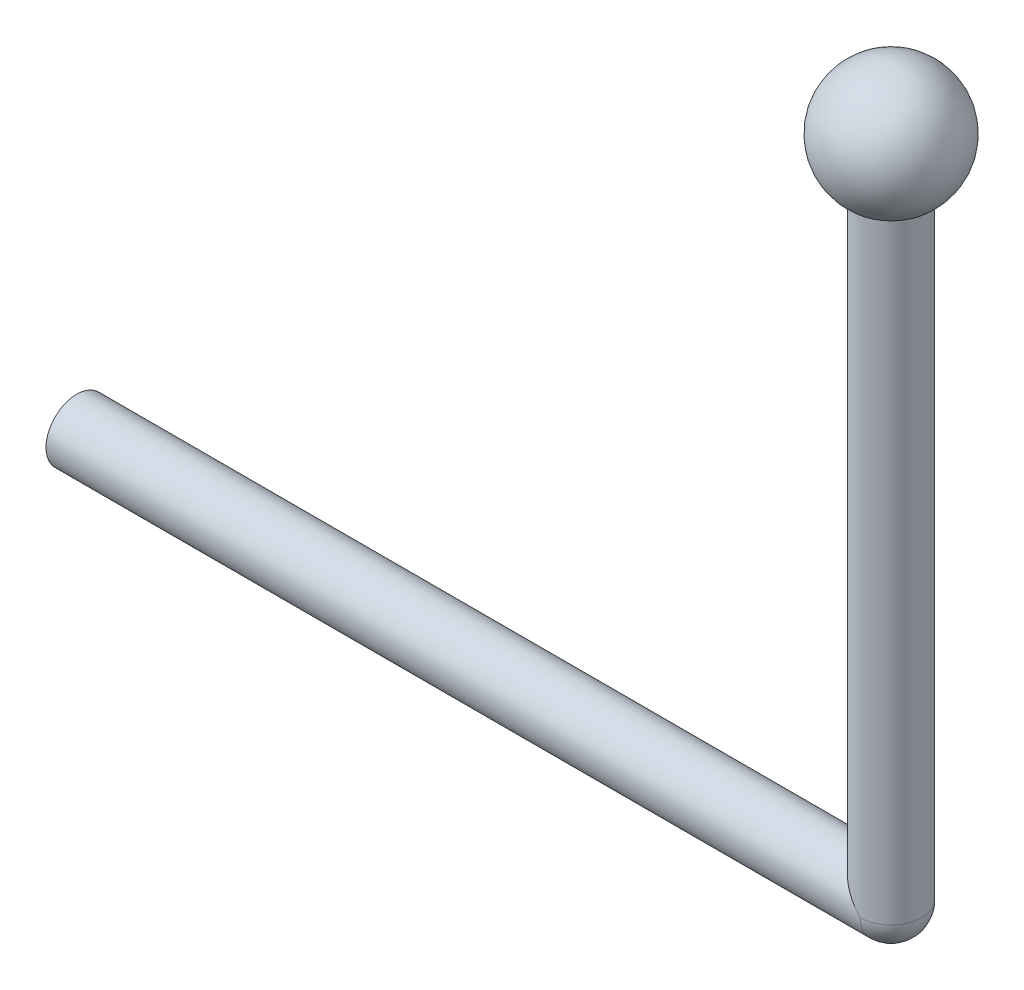
SolidWorks part; units mm, degrees
material "AISI 316 退火不锈钢条 (SS)"
ref_plane "前视基准面" through (0, 0, 0) normal (0, 0, 1) x (1, 0, 0)
ref_plane "上视基准面" through (0, 0, 0) normal (0, 1, 0) x (1, 0, 0)
ref_plane "右视基准面" through (0, 0, 0) normal (1, 0, 0) x (0, 0, -1)
sketch "草图1" plane through (0, 0, 0) normal (0, 0, 1) x (1, 0, 0)
  line L0 (0, 0) -> (0, -4)
  line L1 (0, -4) -> (0, -49)
  line L2 (0, -49) -> (9.6403, -55.4018) construction
  line L3 (-2, 0) -> (-2, -4)
  line L4 (-2, -4) -> (-2, -50.0727)
  line L5 (-2, -50.0727) -> (8.9504, -57.3445) construction
  line L6 (64.448, -62.7045) -> (64.6403, -60.7138)
  line L7 (0, 0) -> (-2, 0)
  line L8 (0, 0) -> (0, 4)
  line L9 (0, -49) -> (60, -49)
  line L10 (-2, 0) -> (-2, -4)
  line L11 (9.6403, -55.4018) -> (64.6403, -60.7138) construction
  line L12 (8.9504, -57.3445) -> (64.448, -62.7045) construction
  line L13 (-2, -4) -> (-2, -51)
  line L14 (-2, -51) -> (60, -51)
  circle A0 centre (0, 0) radius 4
  point P3 (0, -51.839)
  point P7 (6.2479, -54.3857)
  dimension "D1" = 8
  dimension "D2" = 45
  dimension "D3" = 2
  dimension "D5" = 60
  dimension "D4" = 2
revolve "旋转3" add sketch "草图1" angle 360 about L1
sketch "草图3" plane through (0, 0, 0) normal (0, 0, 1) x (1, 0, 0)
  line L0 (0, 0) -> (0, -2)
  line L1 (0, -2) -> (0, -45)
  line L2 (-2, -43) -> (0, -43)
  line L3 (-2, 0) -> (-2, -2)
  line L4 (-2, -2) -> (-2, -43)
  line L6 (-60, -45) -> (-60, -43)
  line L7 (0, 0) -> (-2, 0)
  line L9 (-2, -43) -> (-60, -43) construction
  line L10 (0, -45) -> (-60, -45) construction
  circle A0 centre (0, 0) radius 2
  dimension "D1" = 4
  dimension "D2" = 45
  dimension "D3" = 60
  dimension "D4" = 2
revolve "旋转4" add sketch "草图3" angle 360 about L1
sketch "草图4" plane through (0, -43, 0) normal (0, -1, 0) x (1, 0, 0)
  line L0 (-0.494, 0) -> (2, 0)
  line L1 (-0.494, 0) -> (-52.7788, 0)
  line L2 (-52.7788, 2) -> (-52.7788, 0)
  line L3 (0, 2) -> (2, 2)
  line L4 (0, 2) -> (-0.494, 2)
  line L5 (-0.494, 2) -> (-52.7788, 2)
  line L6 (0, 0) -> (2, 0) construction
  line L7 (0, 0) -> (-0.494, 0) construction
  line L8 (0, 2) -> (0, 0)
  line L9 (0, 0) -> (0, 2)
  circle A1 centre (0, 0) radius 2
  circle A2 centre (0, 0) radius 4
  dimension "D1" = 2
revolve "旋转6" add sketch "草图4" angle 360 about L1
